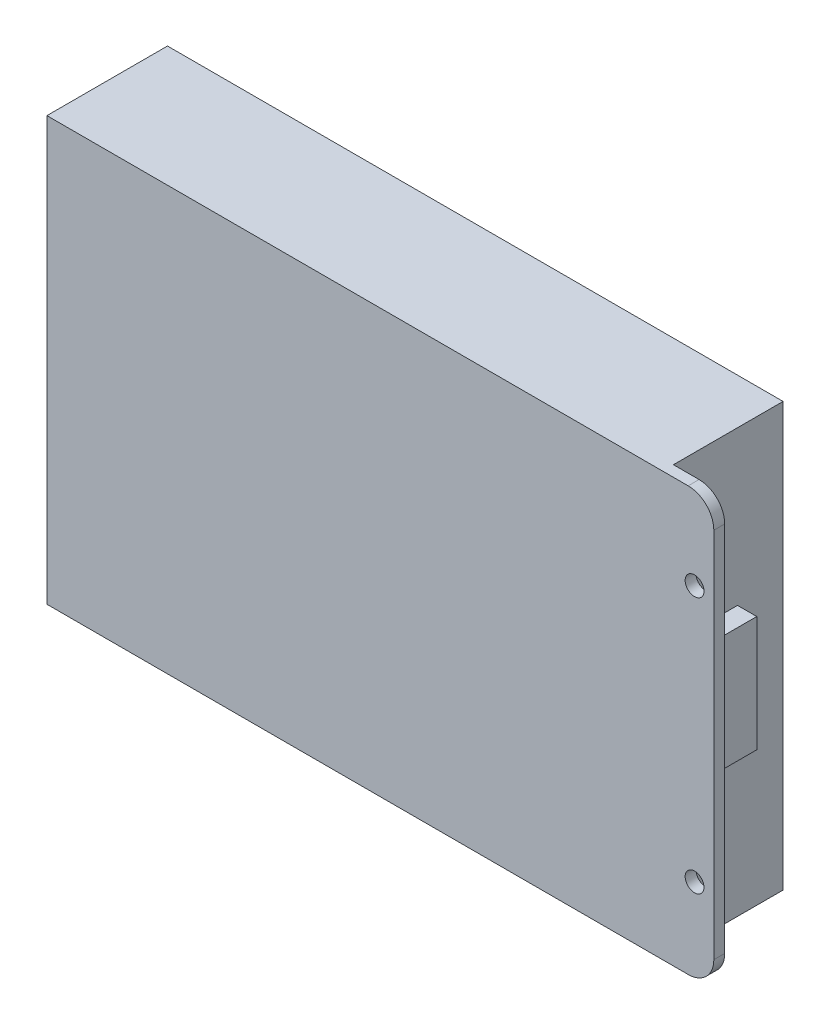
SolidWorks part; units mm, degrees
ref_plane "Front Plane" through (0, 0, 0) normal (0, 0, 1) x (1, 0, 0)
ref_plane "Top Plane" through (0, 0, 0) normal (0, 1, 0) x (1, 0, 0)
ref_plane "Right Plane" through (0, 0, 0) normal (1, 0, 0) x (0, 0, -1)
sketch "Sketch1" plane through (0, 0, 0) normal (0, 0, 1) x (1, 0, 0)
  line L1 (-48, -33) -> (48, -33)
  line L2 (-48, -33) -> (-48, 33)
  line L3 (-48, 33) -> (48, 33)
  line L4 (48, -33) -> (48, 33)
  line L5 (-48, -33) -> (48, 33) construction
  line L6 (-48, 33) -> (48, -33) construction
  point P0 (0, 0)
  dimension "D1" = 96
  dimension "D2" = 66
extrude "Boss-Extrude1" add sketch "Sketch1" along normal blind 17.1
sketch "Sketch2" plane through (0, 0, 17.1) normal (0, 0, 1) x (1, 0, 0)
  line L0 (-48, -33) -> (48, -33) construction
  line L1 (-48, 33) -> (52, 33)
  line L2 (-48, 33) -> (-48, -33)
  line L3 (-48, -33) -> (52, -33)
  line L4 (56, 29) -> (56, -29)
  arc A0 (52, -33) -> (56, -29) centre (52, -29) ccw
  arc A1 (52, 33) -> (56, 29) centre (52, 29) cw
  point P11 (56, 33)
  dimension "D2" = 4
  dimension "D3" = 4
  dimension "D1" = 104
extrude "Boss-Extrude2" add sketch "Sketch2" along normal blind 1.7
sketch "Sketch3" plane through (48, 0, 0) normal (1, 0, 0) x (0, 0, -1)
  line L0 (-17.1, -33) -> (-17.1, 33) construction
  line L1 (-17.1, 9) -> (-7.1, 9)
  line L2 (-17.1, 9) -> (-17.1, -9)
  line L3 (-17.1, -9) -> (-7.1, -9)
  line L4 (-7.1, 9) -> (-7.1, -9)
  line L5 (-7.1, 0) -> (-17.1, 0) construction
  line L6 (-17.1, -33) -> (0, -33) construction
  line L7 (-17.1, 33) -> (0, 33) construction
  dimension "D1" = 18
  dimension "D2" = 10
extrude "Boss-Extrude3" add sketch "Sketch3" along normal blind 3
sketch "Sketch4" plane through (0, 0, 18.8) normal (0, 0, 1) x (1, 0, 0)
  line L0 (53, 33) -> (53, -33) construction
  line L1 (52, 33) -> (-48, 33) construction
  line L2 (-48, -33) -> (52, -33) construction
  line L3 (0, 0) -> (56, 0) construction
  line L4 (56, -29) -> (56, 29) construction
  circle A0 centre (53, 20) radius 1.47
  circle A1 centre (53, -20) radius 1.47
  point P10 (0, 0)
  dimension "D1" = 2.94
  dimension "D2" = 20
  dimension "D3" = 3
extrude "Cut-Extrude1" cut sketch "Sketch4" against normal through all
